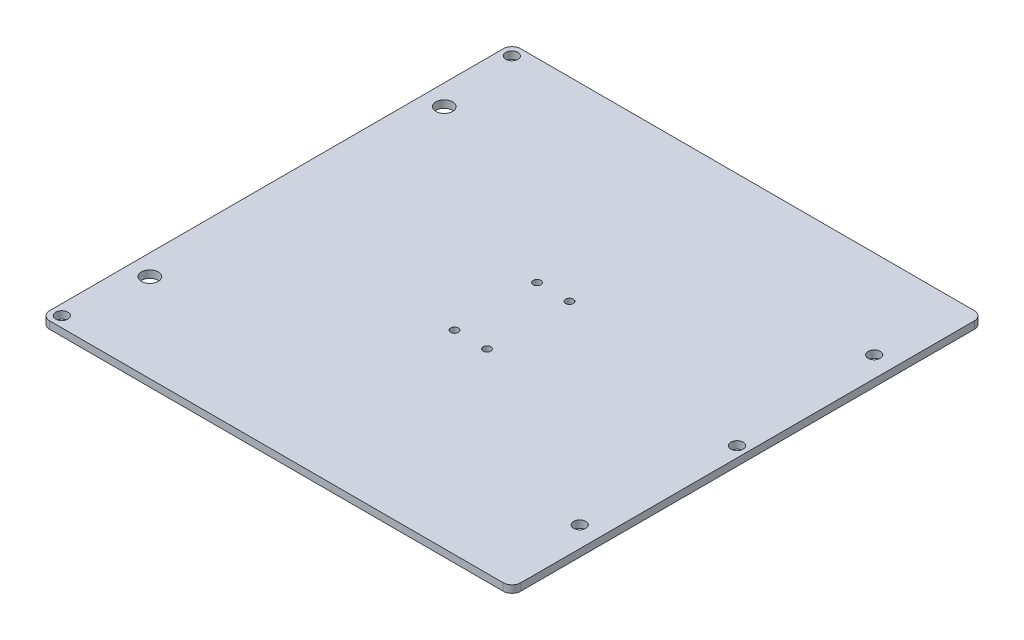
SolidWorks part; units mm, degrees
material "5052-H32"
ref_plane "Front Plane" through (0, 0, 0) normal (0, 0, 1) x (1, 0, 0)
ref_plane "Top Plane" through (0, 0, 0) normal (0, 1, 0) x (1, 0, 0)
ref_plane "Right Plane" through (0, 0, 0) normal (1, 0, 0) x (0, 0, -1)
sketch "Sketch1" plane through (0, 0, 0) normal (0, 1, 0) x (1, 0, 0)
  line L0 (0, 0) -> (203.2, 0)
  line L1 (0, 0) -> (203.2, 0) construction
  line L2 (0, 0) -> (0, 203.2)
  line L3 (0, 203.2) -> (203.2, 203.2)
  line L4 (203.2, 0) -> (203.2, 203.2)
  line L5 (0, 0) -> (203.2, 0) construction
  dimension "D1" = 203.2
  dimension "D2" = 203.2
extrude "Boss-Extrude1" add sketch "Sketch1" along normal blind 3.175
sketch "Sketch2" plane through (0, 3.175, 0) normal (0, 1, 0) x (1, 0, 0)
  line L0 (203.2, 203.2) -> (0, 203.2) construction
  line L1 (0, 0) -> (203.2, 0) construction
  line L2 (203.2, 203.2) -> (0, 203.2) construction
  line L4 (8.9014, 203.2) -> (8.9014, 0) construction
  line L5 (194.2986, 0) -> (194.2986, 203.2) construction
  line L7 (101.6, 203.2) -> (101.6, 0) construction
  circle A0 centre (8.9014, 38.1) radius 3.6
  circle A1 centre (8.9014, 165.1) radius 3.6
  circle A2 centre (194.2986, 38.1) radius 2.625
  circle A3 centre (194.2986, 165.1) radius 2.625
  dimension "D2" = 7.2
  dimension "D5" = 5.25
  dimension "D1" = 185.3971
  dimension "D3" = 38.1
  dimension "D4" = 38.1
extrude "wheel holes" cut sketch "Sketch2" against normal up to next
sketch "Sketch3" plane through (0, 0, 0) normal (0, -1, 0) x (1, 0, 0)
  line L0 (0, -203.2) -> (0, 0) construction
  line L1 (203.2, -203.2) -> (0, -203.2) construction
  line L2 (203.2, 0) -> (203.2, -203.2) construction
  line L4 (0, 0) -> (203.2, 0) construction
  circle A0 centre (4.5009, -4.572) radius 2.625
  circle A1 centre (4.5009, -198.628) radius 2.625
  circle A2 centre (198.628, -101.6) radius 2.625
  dimension "D1" = 5.25
  dimension "D4" = 4.572
  dimension "D2" = 4.572
  dimension "D3" = 4.5009
  dimension "D5" = 4.572
  dimension "D6" = 101.6
extrude "build plate holes" cut sketch "Sketch3" against normal up to next
fillet "Fillet1" radius 3.81 4 edges at (0, 1.5875, -203.2) (203.2, 1.5875, -203.2) (203.2, 1.5875, 0) (0, 1.5875, 0)
sketch "Sketch4" plane through (0, 3.175, 0) normal (0, 1, 0) x (1, 0, 0)
  line L0 (101.6, 0) -> (101.6, 203.2) construction
  line L3 (0, 101.6) -> (203.2, 101.6) construction
  line L6 (3.81, 0) -> (199.39, 0) construction
  line L7 (199.39, 203.2) -> (3.81, 203.2) construction
  line L8 (203.2, 3.81) -> (203.2, 199.39) construction
  circle A0 centre (94.6, 119.38) radius 1.65
  circle A1 centre (108.6, 119.38) radius 1.65
  circle A2 centre (108.6, 83.82) radius 1.65
  circle A3 centre (94.6, 83.82) radius 1.65
  dimension "D1" = 3.3
  dimension "D2" = 14
  dimension "D4" = 17.78
extrude "belt clamp holes" cut sketch "Sketch4" against normal up to next
